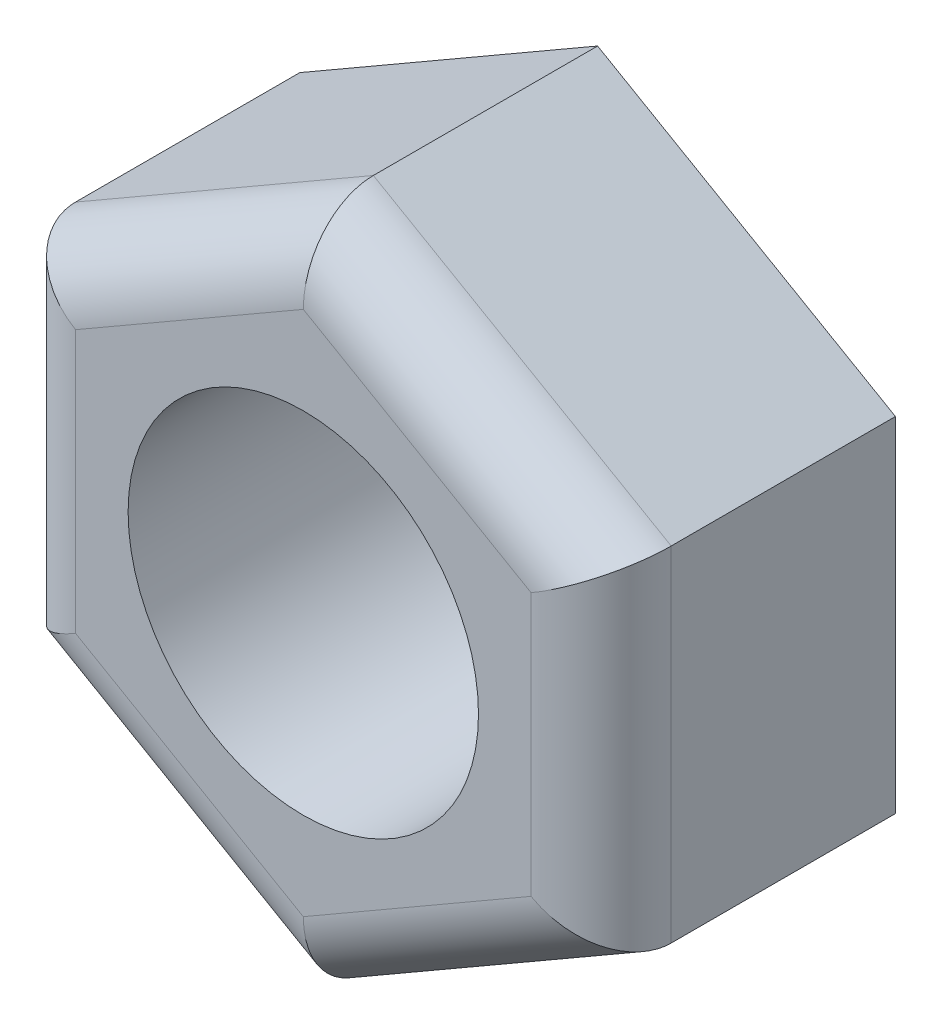
SolidWorks part; units mm, degrees
ref_plane "Plan de face" through (0, 0, 0) normal (0, 0, 1) x (1, 0, 0)
ref_plane "Plan de dessus" through (0, 0, 0) normal (0, 1, 0) x (1, 0, 0)
ref_plane "Plan de droite" through (0, 0, 0) normal (1, 0, 0) x (0, 0, -1)
sketch "Esquisse1" plane through (0, 0, 0) normal (0, 0, 1) x (1, 0, 0)
  line L1 (8.5, 4.9075) -> (0, 9.815)
  line L2 (0, 9.815) -> (-8.5, 4.9075)
  line L3 (-8.5, 4.9075) -> (-8.5, -4.9075)
  line L4 (-8.5, -4.9075) -> (0, -9.815)
  line L5 (0, -9.815) -> (8.5, -4.9075)
  line L6 (8.5, -4.9075) -> (8.5, 4.9075)
  circle A0 centre (0, 0) radius 8.5 construction
  circle A1 centre (0, 0) radius 5
  dimension "D2" = 10
  dimension "D1" = 17
extrude "Boss.-Extru.1" add sketch "Esquisse1" against normal blind 8.4
fillet "Congé2" radius 2 6 edges at (4.25, -7.3612, 0) (8.5, 0, 0) (-4.25, 7.3612, 0) (4.25, 7.3612, 0) (-8.5, 0, 0) (-4.25, -7.3612, 0)
